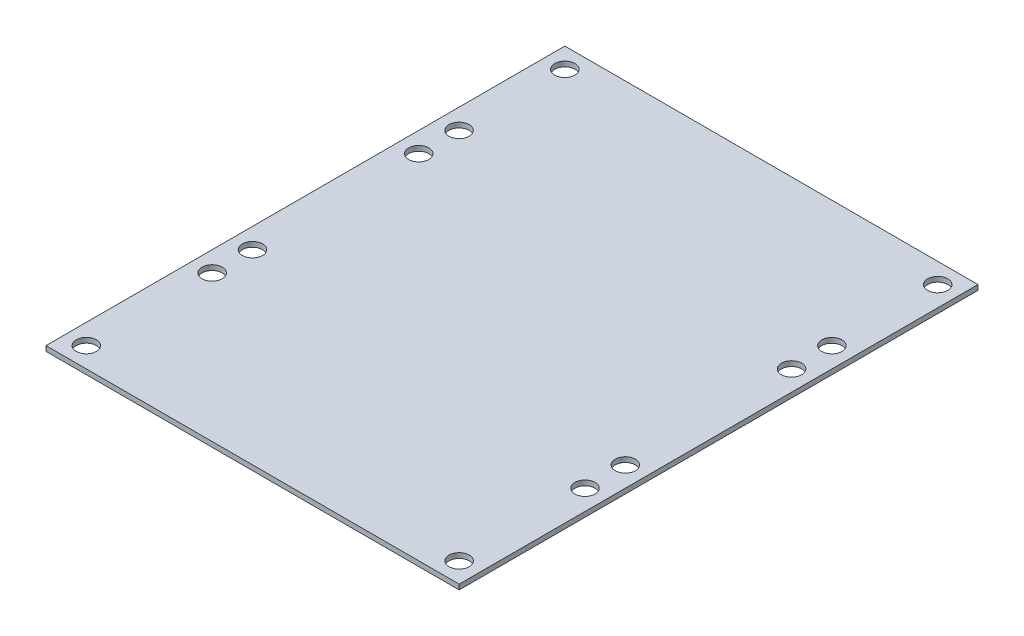
SolidWorks part; units mm, degrees
material "PE High Density"
ref_plane "Front Plane" through (0, 0, 0) normal (0, 0, 1) x (1, 0, 0)
ref_plane "Top Plane" through (0, 0, 0) normal (0, 1, 0) x (1, 0, 0)
ref_plane "Right Plane" through (0, 0, 0) normal (1, 0, 0) x (0, 0, -1)
sketch "Sketch1" plane through (0, 0, 0) normal (0, 1, 0) x (1, 0, 0)
  line L0 (6.35, 157.1244) -> (6.35, 117.4369) construction
  line L1 (0, 0) -> (130.175, 0)
  line L2 (0, 0) -> (0, 163.4744)
  line L3 (0, 163.4744) -> (130.175, 163.4744)
  line L4 (130.175, 0) -> (130.175, 163.4744)
  line L5 (6.35, 117.4369) -> (6.35, 52.3494) construction
  line L6 (65.0875, 0) -> (65.0875, 163.4744) construction
  line L7 (6.35, 52.3494) -> (6.35, 45.9994) construction
  circle A0 centre (6.35, 6.35) radius 3.175
  circle A1 centre (6.35, 157.1244) radius 3.175
  circle A4 centre (123.825, 6.35) radius 3.175
  circle A7 centre (123.825, 157.1244) radius 3.175
  circle A8 centre (6.35, 123.7869) radius 3.175
  circle A9 centre (6.35, 111.0869) radius 3.175
  circle A10 centre (6.35, 58.6994) radius 3.175
  circle A11 centre (6.35, 45.9994) radius 3.175
  circle A12 centre (123.825, 123.7869) radius 3.175
  circle A13 centre (123.825, 111.0869) radius 3.175
  circle A14 centre (123.825, 58.6994) radius 3.175
  circle A15 centre (123.825, 45.9994) radius 3.175
  dimension "D3" = 6.35
  dimension "D4" = 6.35
  dimension "D5" = 6.35
  dimension "D6" = 6.35
  dimension "D7" = 6.35
  dimension "D8" = 6.35
  dimension "D9" = 39.6875
  dimension "D10" = 6.35
  dimension "D12" = 6.35
  dimension "D13" = 6.35
  dimension "D14" = 6.35
  dimension "D15" = 6.35
  dimension "D16" = 6.35
  dimension "D18" = 6.35
  dimension "D1" = 130.175
  dimension "D2" = 163.4744
  dimension "D11" = 65.0875
  dimension "D17" = 6.35
extrude "Boss-Extrude1" add sketch "Sketch1" along normal blind 1.5875
